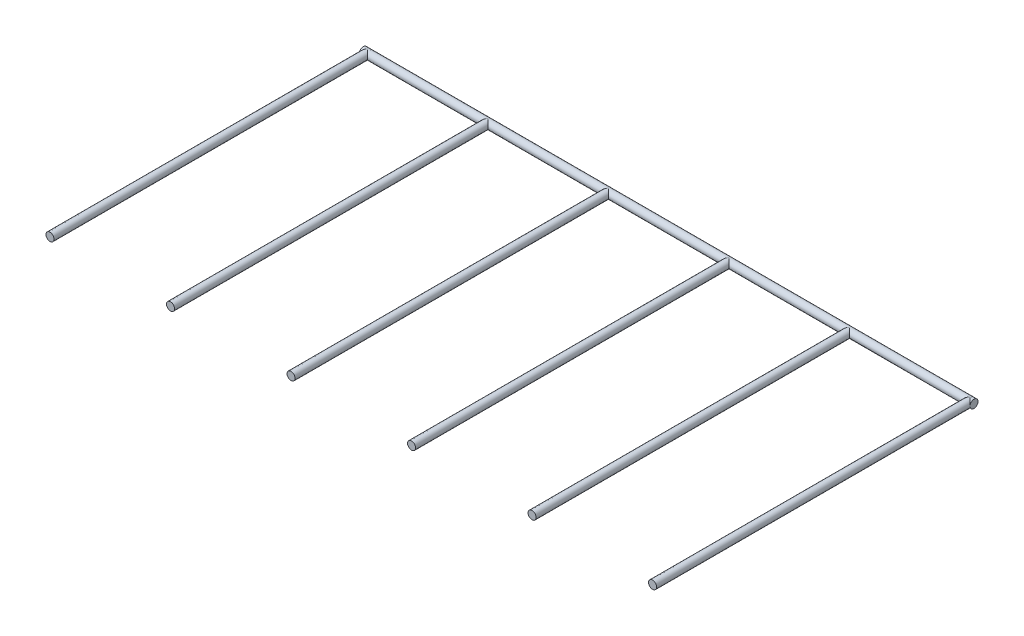
SolidWorks part; units mm, degrees
ref_plane "Front Plane" through (0, 0, 0) normal (0, 0, 1) x (1, 0, 0)
ref_plane "Top Plane" through (0, 0, 0) normal (0, 1, 0) x (1, 0, 0)
ref_plane "Right Plane" through (0, 0, 0) normal (1, 0, 0) x (0, 0, -1)
sketch "Sketch1" plane through (0, 0, 0) normal (1, 0, 0) x (0, 0, -1)
  circle A0 centre (0, 0) radius 1.5875
  dimension "D1" = 3.175
extrude "Boss-Extrude1" add sketch "Sketch1" along normal mid plane 241.3 contours A0
sketch "Sketch3" plane through (0, 0, 0) normal (0, 0, 1) x (1, 0, 0)
  line L0 (-120.65, 1.5875) -> (-120.65, -1.5875) construction
  line L1 (120.65, 1.5875) -> (-120.65, 1.5875) construction
  line L2 (-120.65, -1.5875) -> (120.65, -1.5875) construction
  circle A0 centre (-119.0625, 0) radius 1.5875
extrude "Boss-Extrude2" add sketch "Sketch3" along normal blind 125.4125
pattern_linear "LPattern1" count 6 spacing 47.625 along (1, 0, 0) of "Boss-Extrude2"
